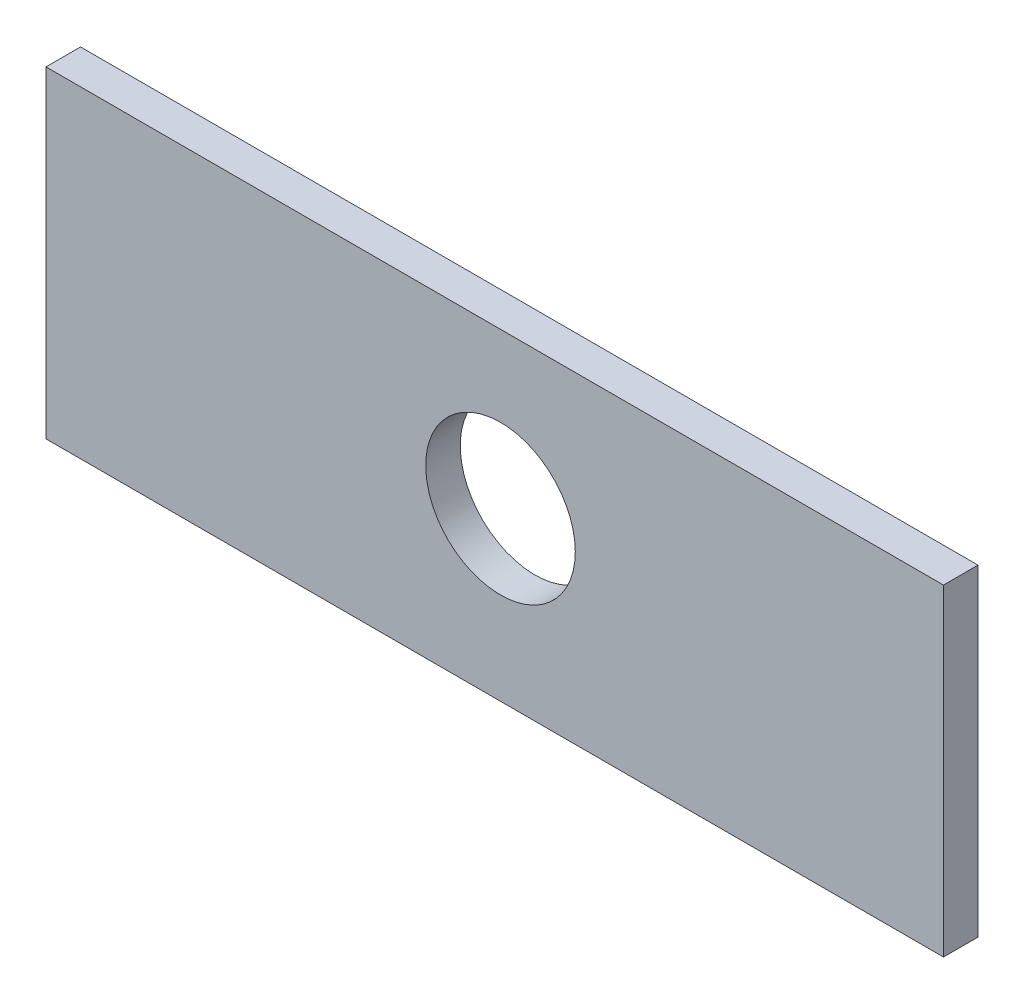
SolidWorks part; units mm, degrees
ref_plane "Front Plane" through (0, 0, 0) normal (0, 0, 1) x (1, 0, 0)
ref_plane "Top Plane" through (0, 0, 0) normal (0, 1, 0) x (1, 0, 0)
ref_plane "Right Plane" through (0, 0, 0) normal (1, 0, 0) x (0, 0, -1)
sketch "Sketch1" plane through (0, 0, 0) normal (0, 0, 1) x (1, 0, 0)
  line L0 (-44.1929, 9.0026) -> (33.8071, 9.0026)
  line L1 (33.8071, 9.0026) -> (33.8071, -18.9974)
  line L2 (33.8071, -18.9974) -> (-44.1929, -18.9974)
  line L3 (-44.1929, 9.0026) -> (-44.1929, -18.9974)
  circle A0 centre (-4.6929, -4.4974) radius 6.5
  dimension "D3" = 13
  dimension "D1" = 78
  dimension "D2" = 28
  dimension "D4" = 14.5
  dimension "D5" = 39.5
extrude "Boss-Extrude1" add sketch "Sketch1" along normal mid plane 3
